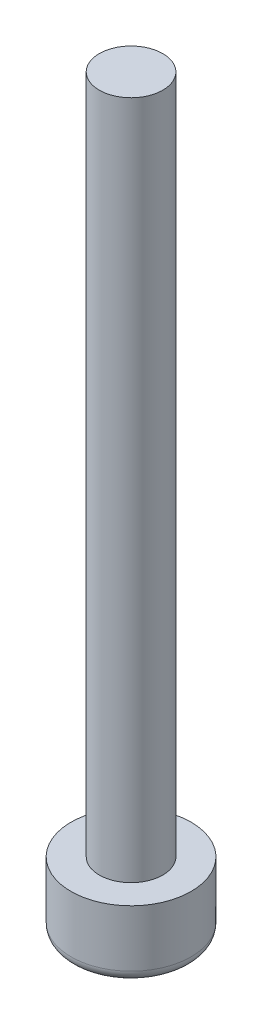
SolidWorks part; units mm, degrees
ref_plane "Front Plane" through (0, 0, 0) normal (0, 0, 1) x (1, 0, 0)
ref_plane "Top Plane" through (0, 0, 0) normal (0, 1, 0) x (1, 0, 0)
ref_plane "Right Plane" through (0, 0, 0) normal (1, 0, 0) x (0, 0, -1)
sketch "Sketch2" plane through (0, 0, 0) normal (0, 0, 1) x (1, 0, 0)
  line L0 (0, 0) -> (0, 25) construction
  line L7 (0, 0) -> (2.65, 0)
  line L8 (2.65, 0) -> (2.65, 3)
  line L9 (2.65, 3) -> (1.4, 3)
  line L10 (1.4, 3) -> (1.4, 33)
  line L11 (1.4, 33) -> (0, 33)
  line L12 (0, 33) -> (0, 0)
  dimension "D1" = 2.65
  dimension "D2" = 1.4
  dimension "D3" = 3
  dimension "D4" = 30
  dimension "D5" = 25
revolve "Revolve1" add sketch "Sketch2" angle 360 about L0
sketch "Sketch3" plane through (0, 0, 0) normal (0, -1, 0) x (1, 0, 0)
  line L1 (-1.4434, 0) -> (-0.7217, -1.25)
  line L2 (-0.7217, -1.25) -> (0.7217, -1.25)
  line L3 (0.7217, -1.25) -> (1.4434, 0)
  line L4 (1.4434, 0) -> (0.7217, 1.25)
  line L5 (0.7217, 1.25) -> (-0.7217, 1.25)
  line L6 (-0.7217, 1.25) -> (-1.4434, 0)
  circle A0 centre (0, 0) radius 1.25 construction
  circle A1 centre (0, 0) radius 1.75 construction
  dimension "D1" = 2.5
  dimension "D2" = 3.5
extrude "Cut-Extrude1" cut sketch "Sketch3" against normal blind 2
ref_plane "Plane1" through (0, 0, 0) normal (0, 0, -1) x (-1, 0, 0)
sketch "Sketch4" plane through (0, 0, 0) normal (0, 0, -1) x (-1, 0, 0)
  line L0 (0, 0) -> (0, 0.3)
  line L1 (-1.75, 0) -> (1.75, 0) construction
  line L2 (0, 0) -> (-1.75, 0)
  line L3 (0, 0.3) -> (1, 0.3) construction
  arc A0 (-1.75, 0) -> (0, 0.3) centre (0, -4.9542) cw
  dimension "D1" = 0.3
  dimension "D2" = 1
revolve "Cut-Revolve1" cut sketch "Sketch4" angle 360 about L0
fillet "Fillet1" radius 0.5 1 edges at (0, 0, -2.65)
